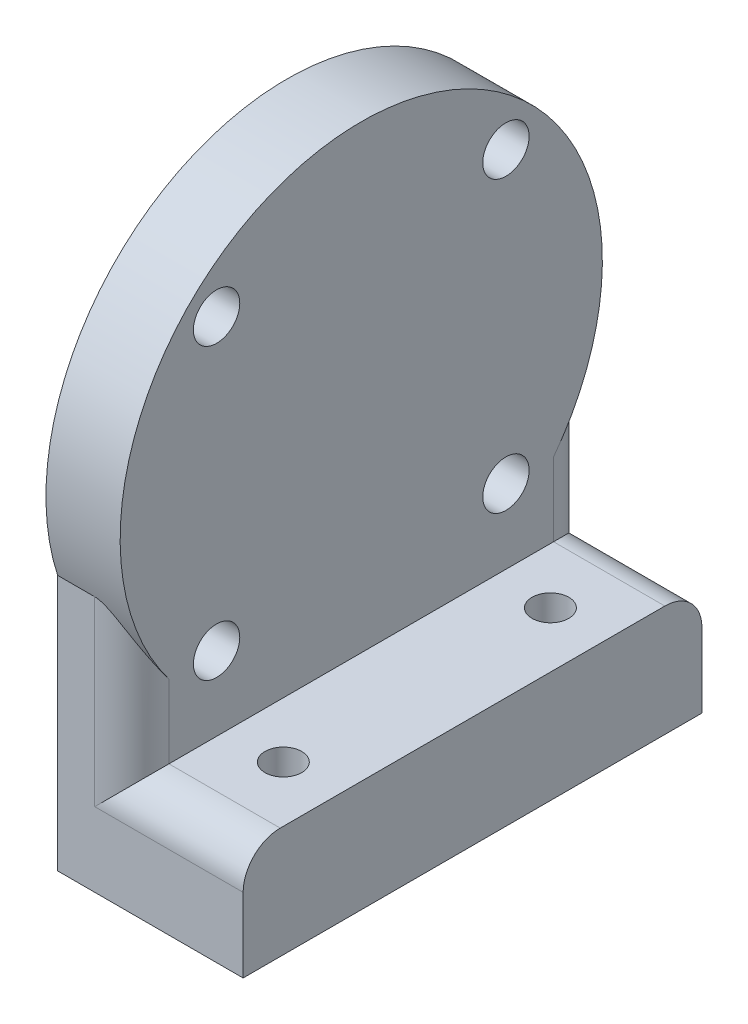
SolidWorks part; units mm, degrees
ref_plane "Front Plane" through (0, 0, 0) normal (0, 0, 1) x (1, 0, 0)
ref_plane "Top Plane" through (0, 0, 0) normal (0, 1, 0) x (1, 0, 0)
ref_plane "Right Plane" through (0, 0, 0) normal (1, 0, 0) x (0, 0, -1)
sketch "Sketch1" plane through (0, 0, 0) normal (1, 0, 0) x (0, 0, -1)
  circle A0 centre (0, 0) radius 32.5
  dimension "D1" = 65
extrude "Boss-Extrude1" add sketch "Sketch1" along normal blind 10
sketch "Sketch2" plane through (10, 0, 0) normal (1, 0, 0) x (0, 0, -1)
  line L0 (0, 0) -> (-22.981, -22.981) construction
  line L1 (0, 0) -> (0, -32.5) construction
  circle A0 centre (0, 0) radius 32.5 construction
  circle A1 centre (-19.502, -19.502) radius 3.125
  circle A2 centre (-19.502, 19.502) radius 3.125
  circle A3 centre (19.502, 19.502) radius 3.125
  circle A4 centre (19.502, -19.502) radius 3.125
  point P9 (0, 0)
  point P18 (0, 0)
  dimension "D3" = 6.25
  dimension "D1" = 45
  dimension "D4" = 27.58
  dimension "D2" = 4
extrude "Cut-Extrude1" cut sketch "Sketch2" against normal through all
sketch "Sketch3" plane through (0, 0, 0) normal (-1, 0, 0) x (0, 0, 1)
  line L0 (-30.9233, -10) -> (-30.9233, -44.5)
  line L1 (-30.9233, -44.5) -> (30.9233, -44.5)
  line L2 (30.9233, -44.5) -> (30.9233, -10)
  line L3 (-30.9233, -10) -> (30.9233, -10) construction
  line L4 (-30.9233, -32.5) -> (30.9233, -32.5) construction
  arc A0 (30.9233, -10) -> (-30.9233, -10) centre (0, 0) cw
  circle A1 centre (0, 0) radius 32.5 construction
  dimension "D2" = 12
  dimension "D1" = 10
extrude "Boss-Extrude2" add sketch "Sketch3" against normal up to surface (10 mm away) separate body up to face at (10, -19.502, -22.627)
sketch "Sketch4" plane through (10, 0, 0) normal (1, 0, 0) x (0, 0, -1)
  line L0 (30.9233, -10) -> (30.9233, -44.5) construction
  line L1 (-30.9233, -44.5) -> (30.9233, -44.5)
  line L2 (-30.9233, -44.5) -> (-30.9233, -29.5)
  line L3 (-30.9233, -29.5) -> (30.9233, -29.5)
  line L4 (30.9233, -44.5) -> (30.9233, -29.5)
  dimension "D1" = 15
extrude "Boss-Extrude3" add sketch "Sketch4" along normal blind 15
sketch "Sketch5" plane through (0, -29.5, 0) normal (0, 1, 0) x (1, 0, 0)
  line L0 (10, -18) -> (25, -18) construction
  line L1 (10, 30.9233) -> (10, -30.9233) construction
  line L2 (25, 30.9233) -> (25, -30.9233) construction
  line L3 (10, 0) -> (25, 0) construction
  circle A0 centre (17.5, -18) radius 2.475
  circle A1 centre (17.5, 18) radius 2.475
  dimension "D1" = 4.95
  dimension "D2" = 18
extrude "Cut-Extrude2" cut sketch "Sketch5" against normal through all
fillet "Fillet1" radius 5 4 edges at (17.5, -29.5, -30.9233) (17.5, -29.5, 30.9233) (10, -19.75, -30.9233) (10, -19.75, 30.9233)
